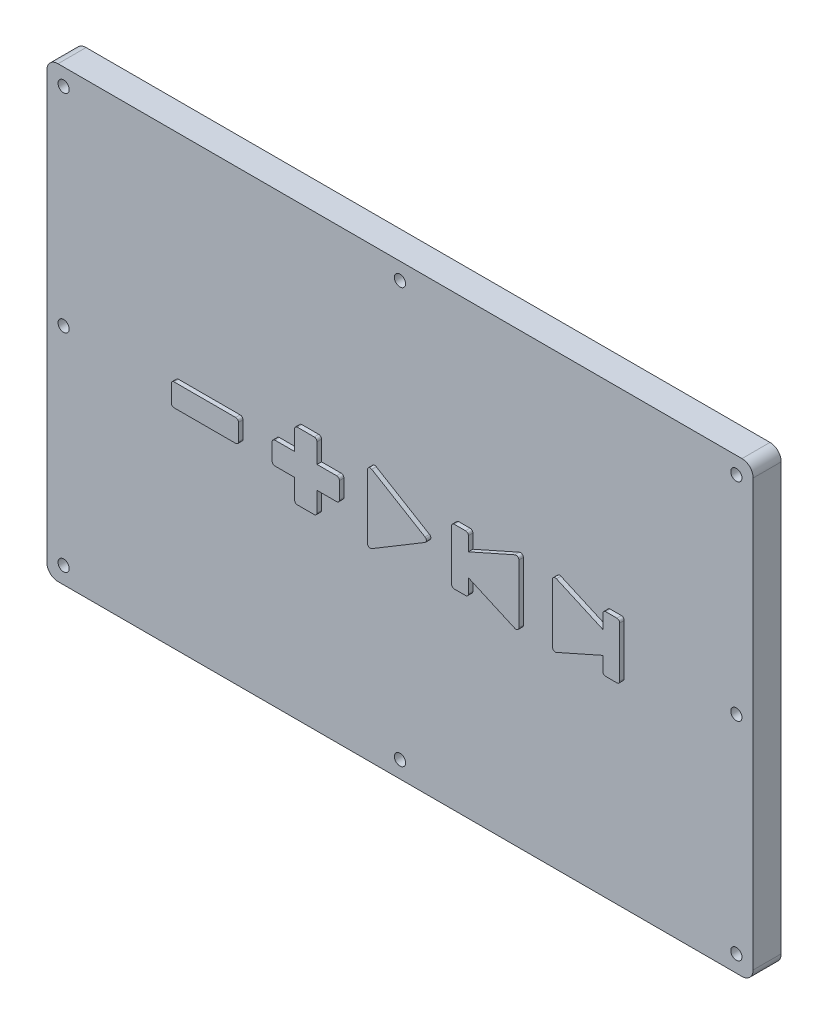
SolidWorks part; units mm, degrees
ref_plane "Front Plane" through (0, 0, 0) normal (0, 0, 1) x (1, 0, 0)
ref_plane "Top Plane" through (0, 0, 0) normal (0, 1, 0) x (1, 0, 0)
ref_plane "Right Plane" through (0, 0, 0) normal (1, 0, 0) x (0, 0, -1)
sketch "Sketch1" plane through (0, 0, 0) normal (0, 0, 1) x (1, 0, 0)
  line L1 (-61, 40) -> (61, 40)
  line L2 (-63, 38) -> (-63, -38)
  line L3 (-61, -40) -> (61, -40)
  line L4 (63, 38) -> (63, -38)
  line L5 (-63, 40) -> (63, -40) construction
  line L6 (-63, -40) -> (63, 40) construction
  arc A0 (61, 40) -> (63, 38) centre (61, 38) cw
  arc A1 (63, -38) -> (61, -40) centre (61, -38) cw
  arc A2 (-61, -40) -> (-63, -38) centre (-61, -38) cw
  arc A3 (-63, 38) -> (-61, 40) centre (-61, 38) cw
  point P0 (0, 0)
  dimension "D1" = 2
sketch "Sketch2" [suppressed] plane through (0, 0, 0) normal (0, 0, 1) x (1, 0, 0)
  line L0 (-5, 5.1169) -> (-5, -5.1169)
  line L1 (-4.2428, -5.5457) -> (4.2854, -0.4287)
  line L2 (4.2854, 0.4287) -> (-4.2428, 5.5457)
  line L3 (-10, -1.5) -> (-10, 1.5)
  line L4 (-10.5, 2) -> (-14, 2)
  line L5 (-14, 2) -> (-14, 5.5)
  line L6 (-14.5, 6) -> (-17.5, 6)
  line L7 (-18, 5.5) -> (-18, 2)
  line L8 (-18, 2) -> (-21.5, 2)
  line L9 (-22, 1.5) -> (-22, -1.5)
  line L10 (-21.5, -2) -> (-18, -2)
  line L11 (-18, -2) -> (-18, -5.5)
  line L12 (-17.5, -6) -> (-14.5, -6)
  line L13 (-14, -5.5) -> (-14, -2)
  line L14 (-14, -2) -> (-10.5, -2)
  line L15 (-28, 1.5) -> (-28, -1.5)
  line L16 (-28.5, -2) -> (-39.5, -2)
  line L17 (-40, -1.5) -> (-40, 1.5)
  line L18 (-39.5, 2) -> (-28.5, 2)
  line L19 (10, 4.5) -> (10, -4.5)
  line L20 (10.5, -5) -> (12.5, -5)
  line L21 (13, -4.5) -> (13, -2)
  line L22 (12.5, 5) -> (10.5, 5)
  line L23 (28, 5.2306) -> (28, -5.2306)
  line L24 (21.2969, 5.6875) -> (13, 2)
  line L25 (13, -2) -> (21.2969, -5.6875)
  line L26 (22, -5.2306) -> (22, 5.2306)
  line L27 (13, 2) -> (13, 4.5)
  line L28 (28.7031, -5.6875) -> (37, -2)
  line L29 (28.7031, 5.6875) -> (37, 2)
  line L30 (37, 2) -> (37, 4.5)
  line L31 (37.5, 5) -> (39.5, 5)
  line L32 (40, 4.5) -> (40, -4.5)
  line L33 (39.5, -5) -> (37.5, -5)
  line L34 (37, -4.5) -> (37, -2)
  arc A0 (-39.5, -2) -> (-40, -1.5) centre (-39.5, -1.5) cw
  arc A1 (-40, 1.5) -> (-39.5, 2) centre (-39.5, 1.5) cw
  arc A2 (-28.5, 2) -> (-28, 1.5) centre (-28.5, 1.5) cw
  arc A3 (-28, -1.5) -> (-28.5, -2) centre (-28.5, -1.5) cw
  arc A4 (-14.5, -6) -> (-14, -5.5) centre (-14.5, -5.5) ccw
  arc A5 (-17.5, -6) -> (-18, -5.5) centre (-17.5, -5.5) cw
  arc A6 (-21.5, -2) -> (-22, -1.5) centre (-21.5, -1.5) cw
  arc A7 (-22, 1.5) -> (-21.5, 2) centre (-21.5, 1.5) cw
  arc A8 (-18, 5.5) -> (-17.5, 6) centre (-17.5, 5.5) cw
  arc A9 (-14.5, 6) -> (-14, 5.5) centre (-14.5, 5.5) cw
  arc A10 (-10.5, 2) -> (-10, 1.5) centre (-10.5, 1.5) cw
  arc A11 (-10.5, -2) -> (-10, -1.5) centre (-10.5, -1.5) ccw
  arc A12 (-4.2428, -5.5457) -> (-5, -5.1169) centre (-4.5, -5.1169) cw
  arc A13 (-5, 5.1169) -> (-4.2428, 5.5457) centre (-4.5, 5.1169) cw
  arc A14 (4.2854, -0.4287) -> (4.2854, 0.4287) centre (4.0282, 0) ccw
  arc A15 (21.2969, 5.6875) -> (22, 5.2306) centre (21.5, 5.2306) cw
  arc A16 (22, -5.2306) -> (21.2969, -5.6875) centre (21.5, -5.2306) cw
  arc A17 (12.5, -5) -> (13, -4.5) centre (12.5, -4.5) ccw
  arc A18 (10.5, -5) -> (10, -4.5) centre (10.5, -4.5) cw
  arc A19 (10, 4.5) -> (10.5, 5) centre (10.5, 4.5) cw
  arc A20 (12.5, 5) -> (13, 4.5) centre (12.5, 4.5) cw
  arc A21 (28.7031, -5.6875) -> (28, -5.2306) centre (28.5, -5.2306) cw
  arc A22 (28, 5.2306) -> (28.7031, 5.6875) centre (28.5, 5.2306) cw
  arc A23 (37.5, -5) -> (37, -4.5) centre (37.5, -4.5) cw
  arc A24 (39.5, -5) -> (40, -4.5) centre (39.5, -4.5) ccw
  arc A25 (37, 4.5) -> (37.5, 5) centre (37.5, 4.5) cw
  arc A26 (40, 4.5) -> (39.5, 5) centre (39.5, 4.5) ccw
  dimension "D1" = 0.5
sketch "Sketch5" [suppressed] plane through (0, 0, 0) normal (0, 0, 1) x (1, 0, 0)
  line L0 (-21, 1) -> (-17, 1)
  line L1 (-39, 1) -> (-29, 1)
  line L2 (-39, 1) -> (-39, -1)
  line L3 (-39, -1) -> (-29, -1)
  line L4 (-29, 1) -> (-29, -1)
  line L5 (-17, 1) -> (-17, 5)
  line L6 (-17, 5) -> (-15, 5)
  line L7 (-15, 5) -> (-15, 1)
  line L8 (-15, 1) -> (-11, 1)
  line L9 (-11, 1) -> (-11, -1)
  line L10 (-11, -1) -> (-15, -1)
  line L11 (-15, -1) -> (-15, -5)
  line L12 (-15, -5) -> (-17, -5)
  line L13 (-17, -5) -> (-17, -1)
  line L14 (-17, -1) -> (-21, -1)
  line L15 (-21, -1) -> (-21, 1)
  line L16 (-4, 4) -> (-4, -4)
  line L17 (-4, -4) -> (3, 0)
  line L18 (3, 0) -> (-4, 4)
  line L19 (29, 4) -> (29, -4)
  line L20 (29, -4) -> (39, 0)
  line L21 (39, 0) -> (29, 4)
  line L22 (11, 0) -> (21, -4)
  line L23 (21, -4) -> (21, 4)
  line L24 (21, 4) -> (11, 0)
sketch "Sketch15" plane through (0, 0, 0) normal (0, 0, 1) x (1, 0, 0)
  circle A0 centre (-52.5, -27.5) radius 1
  circle A1 centre (-52.5, 27.5) radius 1
  circle A2 centre (52.5, -27.5) radius 1
  circle A3 centre (52.5, 27.5) radius 1
  point P0 (0, 0)
sketch "Sketch18" plane through (0, 0, 0) normal (0, 0, 1) x (1, 0, 0)
  circle A0 centre (60, 37) radius 1
  circle A1 centre (60, -37) radius 1
  circle A2 centre (-60, -37) radius 1
  circle A3 centre (-60, 37) radius 1
  circle A4 centre (0, 37) radius 1
  circle A5 centre (0, -37) radius 1
  circle A6 centre (-60, 0) radius 1
  circle A7 centre (60, 0) radius 1
extrude "Boss-Extrude1" add sketch "Sketch1" along normal blind 5
ref_plane "Plane1" through (0, 0, 5) normal (0, 0, 1) x (1, 0, 0)
sketch "Sketch19" plane through (0, 0, 5) normal (0, 0, 1) x (1, 0, 0)
  line L0 (-5, 5.7) -> (-5, -5.7)
  line L1 (-4.2428, -6.1287) -> (5.2572, -0.4287)
  line L2 (5.2572, 0.4287) -> (-4.2428, 6.1287)
  line L3 (-10, -1.5) -> (-10, 1.5)
  line L4 (-10.5, 2) -> (-14, 2)
  line L5 (-14, 2) -> (-14, 5.5)
  line L6 (-14.5, 6) -> (-17.5, 6)
  line L7 (-18, 5.5) -> (-18, 2)
  line L8 (-18, 2) -> (-21.5, 2)
  line L9 (-22, 1.5) -> (-22, -1.5)
  line L10 (-21.5, -2) -> (-18, -2)
  line L11 (-18, -2) -> (-18, -5.5)
  line L12 (-17.5, -6) -> (-14.5, -6)
  line L13 (-14, -5.5) -> (-14, -2)
  line L14 (-14, -2) -> (-10.5, -2)
  line L15 (-28, 1.5) -> (-28, -1.5)
  line L16 (-28.5, -2) -> (-39.5, -2)
  line L17 (-40, -1.5) -> (-40, 1.5)
  line L18 (-39.5, 2) -> (-28.5, 2)
  line L19 (10, 4.5) -> (10, -4.5)
  line L20 (10.5, -5) -> (12.5, -5)
  line L21 (13, -4.5) -> (13, -2)
  line L22 (12.5, 5) -> (10.5, 5)
  line L23 (28, 5.2306) -> (28, -5.2306)
  line L24 (21.2969, 5.6875) -> (13, 2)
  line L25 (13, -2) -> (21.2969, -5.6875)
  line L26 (22, -5.2306) -> (22, 5.2306)
  line L27 (13, 2) -> (13, 4.5)
  line L28 (28.7031, -5.6875) -> (37, -2)
  line L29 (28.7031, 5.6875) -> (37, 2)
  line L30 (37, 2) -> (37, 4.5)
  line L31 (37.5, 5) -> (39.5, 5)
  line L32 (40, 4.5) -> (40, -4.5)
  line L33 (39.5, -5) -> (37.5, -5)
  line L34 (37, -4.5) -> (37, -2)
  arc A0 (-39.5, -2) -> (-40, -1.5) centre (-39.5, -1.5) cw
  arc A1 (-40, 1.5) -> (-39.5, 2) centre (-39.5, 1.5) cw
  arc A2 (-28.5, 2) -> (-28, 1.5) centre (-28.5, 1.5) cw
  arc A3 (-28, -1.5) -> (-28.5, -2) centre (-28.5, -1.5) cw
  arc A4 (-14.5, -6) -> (-14, -5.5) centre (-14.5, -5.5) ccw
  arc A5 (-17.5, -6) -> (-18, -5.5) centre (-17.5, -5.5) cw
  arc A6 (-21.5, -2) -> (-22, -1.5) centre (-21.5, -1.5) cw
  arc A7 (-22, 1.5) -> (-21.5, 2) centre (-21.5, 1.5) cw
  arc A8 (-18, 5.5) -> (-17.5, 6) centre (-17.5, 5.5) cw
  arc A9 (-14.5, 6) -> (-14, 5.5) centre (-14.5, 5.5) cw
  arc A10 (-10.5, 2) -> (-10, 1.5) centre (-10.5, 1.5) cw
  arc A11 (-10.5, -2) -> (-10, -1.5) centre (-10.5, -1.5) ccw
  arc A12 (-4.2428, -6.1287) -> (-5, -5.7) centre (-4.5, -5.7) cw
  arc A13 (-5, 5.7) -> (-4.2428, 6.1287) centre (-4.5, 5.7) cw
  arc A14 (5.2572, -0.4287) -> (5.2572, 0.4287) centre (5, 0) ccw
  arc A15 (21.2969, 5.6875) -> (22, 5.2306) centre (21.5, 5.2306) cw
  arc A16 (22, -5.2306) -> (21.2969, -5.6875) centre (21.5, -5.2306) cw
  arc A17 (12.5, -5) -> (13, -4.5) centre (12.5, -4.5) ccw
  arc A18 (10.5, -5) -> (10, -4.5) centre (10.5, -4.5) cw
  arc A19 (10, 4.5) -> (10.5, 5) centre (10.5, 4.5) cw
  arc A20 (12.5, 5) -> (13, 4.5) centre (12.5, 4.5) cw
  arc A21 (28.7031, -5.6875) -> (28, -5.2306) centre (28.5, -5.2306) cw
  arc A22 (28, 5.2306) -> (28.7031, 5.6875) centre (28.5, 5.2306) cw
  arc A23 (37.5, -5) -> (37, -4.5) centre (37.5, -4.5) cw
  arc A24 (39.5, -5) -> (40, -4.5) centre (39.5, -4.5) ccw
  arc A25 (37, 4.5) -> (37.5, 5) centre (37.5, 4.5) cw
  arc A26 (40, 4.5) -> (39.5, 5) centre (39.5, 4.5) ccw
  dimension "D1" = 0.5
sketch "Sketch20" plane through (0, 0, 5) normal (0, 0, 1) x (1, 0, 0)
  line L35 (-4.1, 4.9935) -> (-4.1, -4.9935)
  line L36 (-4.1, -4.9935) -> (4.2225, 0)
  line L37 (4.2225, 0) -> (-4.1, 4.9935)
  line L38 (-10.9, -1.1) -> (-10.9, 1.1)
  line L39 (-10.9, 1.1) -> (-14.9, 1.1)
  line L40 (-14.9, 1.1) -> (-14.9, 5.1)
  line L41 (-14.9, 5.1) -> (-17.1, 5.1)
  line L42 (-17.1, 5.1) -> (-17.1, 1.1)
  line L43 (-17.1, 1.1) -> (-21.1, 1.1)
  line L44 (-21.1, 1.1) -> (-21.1, -1.1)
  line L45 (-21.1, -1.1) -> (-17.1, -1.1)
  line L46 (-17.1, -1.1) -> (-17.1, -5.1)
  line L47 (-17.1, -5.1) -> (-14.9, -5.1)
  line L48 (-14.9, -5.1) -> (-14.9, -1.1)
  line L49 (-14.9, -1.1) -> (-10.9, -1.1)
  line L50 (-28.9, 1.1) -> (-28.9, -1.1)
  line L51 (-28.9, -1.1) -> (-39.1, -1.1)
  line L52 (-39.1, -1.1) -> (-39.1, 1.1)
  line L53 (-39.1, 1.1) -> (-28.9, 1.1)
  line L54 (10.9, 4.1) -> (10.9, -4.1)
  line L55 (10.9, -4.1) -> (12.1, -4.1)
  line L56 (12.1, -4.1) -> (12.1, -0.6151)
  line L57 (12.1, -0.6151) -> (21.1, -4.6151)
  line L58 (21.1, -4.6151) -> (21.1, 4.6151)
  line L59 (21.1, 4.6151) -> (12.1, 0.6151)
  line L60 (12.1, 0.6151) -> (12.1, 4.1)
  line L61 (12.1, 4.1) -> (10.9, 4.1)
  line L62 (28.9, 4.6151) -> (28.9, -4.6151)
  line L63 (28.9, -4.6151) -> (37.9, -0.6151)
  line L64 (37.9, -4.1) -> (37.9, -0.6151)
  line L65 (39.1, -4.1) -> (37.9, -4.1)
  line L66 (39.1, 4.1) -> (39.1, -4.1)
  line L67 (37.9, 4.1) -> (39.1, 4.1)
  line L68 (37.9, 0.6151) -> (37.9, 4.1)
  line L69 (28.9, 4.6151) -> (37.9, 0.6151)
sketch "Sketch21" plane through (0, 0, 5) normal (0, 0, 1) x (1, 0, 0)
  circle A0 centre (-1, 0) radius 1
  circle A1 centre (-16, 0) radius 1
  circle A2 centre (-34, 0) radius 1
  circle A3 centre (17, 0) radius 1
  circle A4 centre (33, 0) radius 1
sketch "Sketch22" plane through (0, 0, 0) normal (0, 0, 1) x (1, 0, 0)
  circle A0 centre (-34, 0) radius 0.75
  circle A1 centre (-16, 0) radius 0.75
  circle A2 centre (-1, 0) radius 0.75
  circle A3 centre (17, 0) radius 0.75
  circle A4 centre (33, 0) radius 0.75
extrude "Boss-Extrude2" add sketch "Sketch19" along normal blind 0.8
extrude "Cut-Extrude1" cut sketch "Sketch22" along normal blind 1
extrude "Cut-Extrude2" cut sketch "Sketch18" along normal blind 35
extrude "Cut-Extrude3" cut sketch "Sketch15" along normal blind 3
